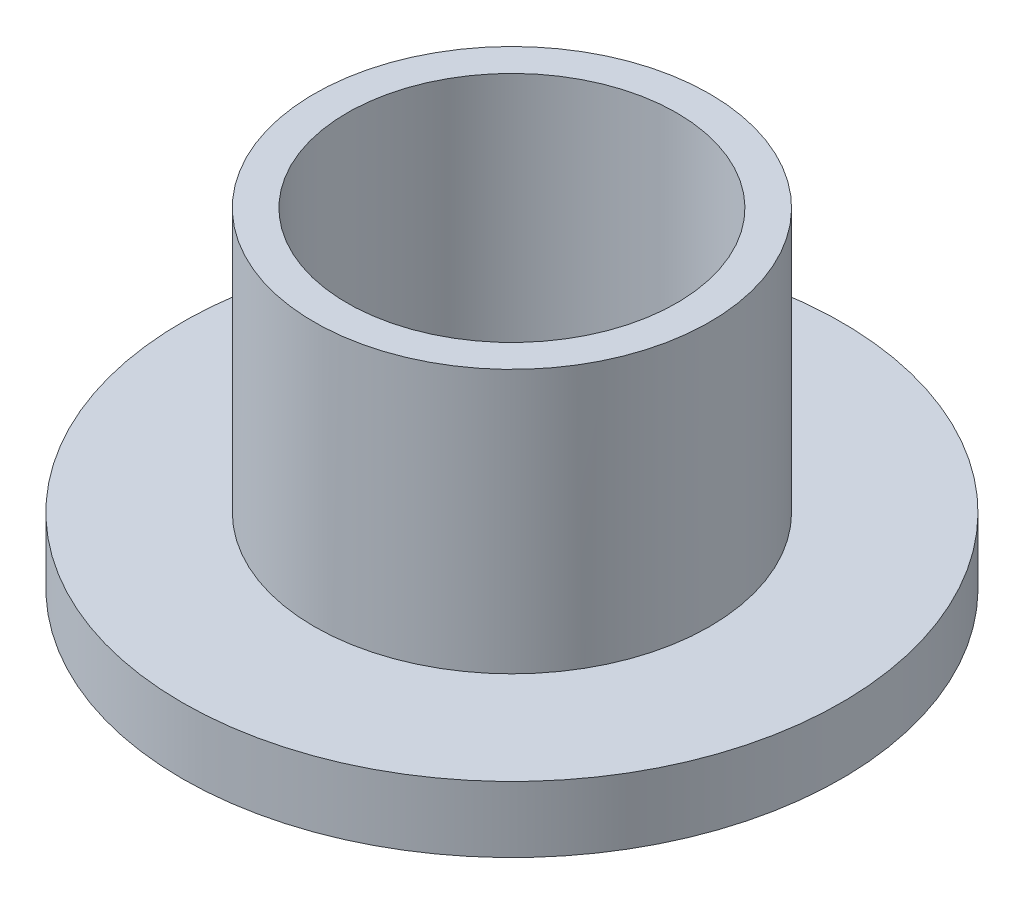
SolidWorks part; units mm, degrees
material "2.0402 (CuZn40Pb2)"
ref_plane "Front Plane" through (0, 0, 0) normal (0, 0, 1) x (1, 0, 0)
ref_plane "Top Plane" through (0, 0, 0) normal (0, 1, 0) x (1, 0, 0)
ref_plane "Right Plane" through (0, 0, 0) normal (1, 0, 0) x (0, 0, -1)
sketch "Sketch1" plane through (0, 0, 0) normal (0, 1, 0) x (1, 0, 0)
  circle A0 centre (0, 0) radius 10
  dimension "D1" = 20
extrude "Boss-Extrude1" add sketch "Sketch1" along normal blind 2
sketch "Sketch3" plane through (0, 0, 0) normal (0, -1, 0) x (1, 0, 0)
  circle A0 centre (0, 0) radius 6
  circle A1 centre (0, 0) radius 5
  point P4 (-23.477, -2.0839)
extrude "Boss-Extrude2" add sketch "Sketch3" against normal blind 10
sketch "Sketch4" plane through (0, 0, 0) normal (0, -1, 0) x (1, 0, 0)
  circle A0 centre (0, 0) radius 5
extrude "Cut-Extrude2" cut sketch "Sketch4" against normal blind 10
